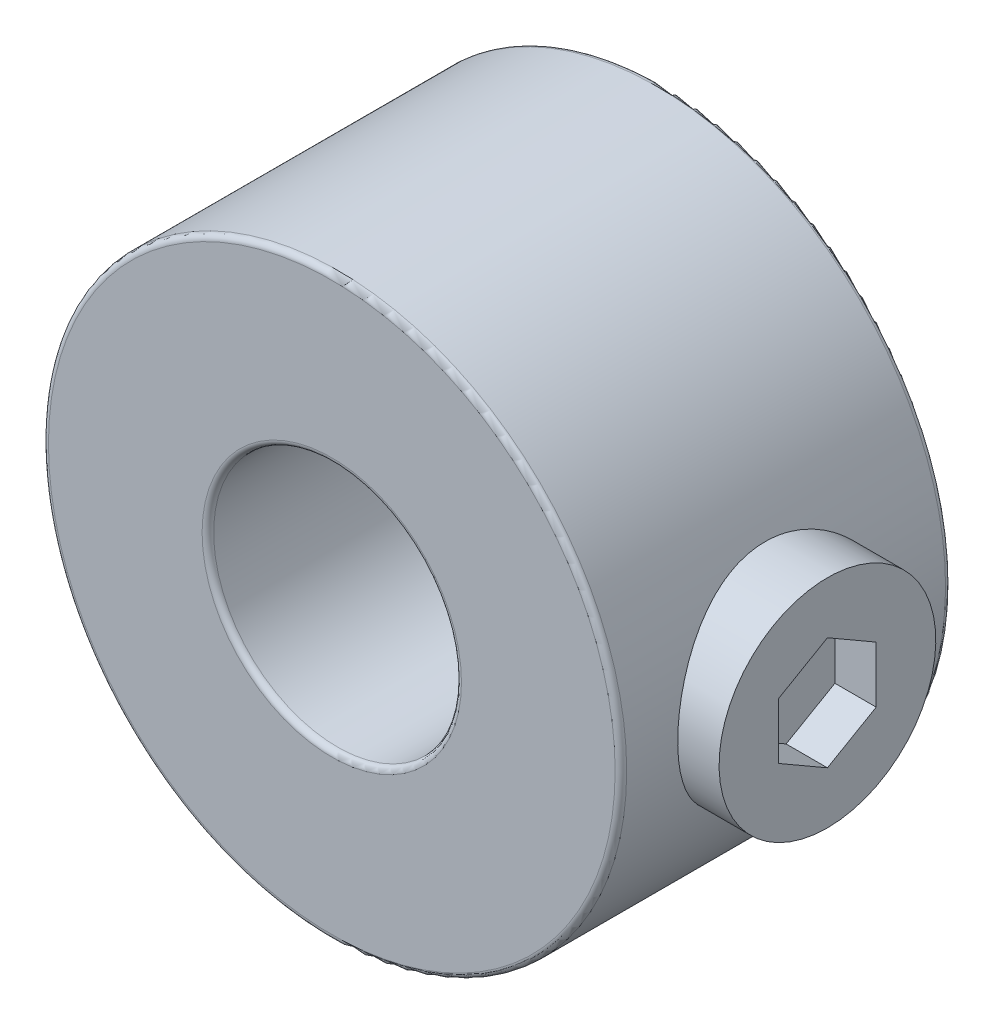
SolidWorks part; units mm, degrees
ref_plane "Front Plane" through (0, 0, 0) normal (0, 0, 1) x (1, 0, 0)
ref_plane "Top Plane" through (0, 0, 0) normal (0, 1, 0) x (1, 0, 0)
ref_plane "Right Plane" through (0, 0, 0) normal (1, 0, 0) x (0, 0, -1)
sketch "Sketch1" plane through (0, 0, 0) normal (0, 0, 1) x (1, 0, 0)
  circle A0 centre (0, 0) radius 5.5562
  circle A1 centre (0, 0) radius 2.3813
  point P4 (5.5562, 0)
  dimension "Bore Dia" = 4.7625
  dimension "OD" = 11.1125
extrude "Extrude1" add sketch "Sketch1" along normal blind 6.35
ref_plane "Plane1" through (5.5562, 0, 0) normal (1, 0, 0) x (0, 0, -1)
sketch "Sketch2" plane through (5.5562, 0, 0) normal (1, 0, 0) x (0, 0, -1)
  line L0 (0, 0) -> (-6.35, 0) construction
  line L1 (-6.35, 5.5562) -> (-6.35, -5.5562) construction
  circle A0 centre (-3.175, 0) radius 2.0828
  dimension "Set Screw Dia" = 4.1656
extrude "Cut-Extrude1" cut sketch "Sketch2" against normal up to surface (5.5562 mm away) up to plane "Right Plane"
ref_plane "Plane2" through (0, 0, 3.175) normal (0, 0, 1) x (1, 0, 0)
sketch "Sketch3" plane through (0, 0, 3.175) normal (0, 0, 1) x (1, 0, 0)
  line L1 (3.175, 0) -> (6.35, 0)
  line L2 (3.175, 0) -> (3.175, 2.0828)
  line L3 (3.175, 2.0828) -> (6.35, 2.0828)
  line L4 (6.35, 0) -> (6.35, 2.0828)
  line L5 (3.175, 0) -> (0, 0) construction
  dimension "D1" = 3.175
  dimension "D2" = 0.7937
  dimension "D3" = 4.1656
revolve "Revolve1" add sketch "Sketch3" angle 360 about L1
sketch "Sketch4" plane through (6.35, 0, 0) normal (1, 0, 0) x (0, 0, -1)
  line L1 (-3.175, 1.0823) -> (-4.1123, 0.5411)
  line L2 (-4.1123, 0.5411) -> (-4.1123, -0.5411)
  line L3 (-4.1123, -0.5411) -> (-3.175, -1.0823)
  line L4 (-3.175, -1.0823) -> (-2.2377, -0.5411)
  line L5 (-2.2377, -0.5411) -> (-2.2377, 0.5411)
  line L6 (-2.2377, 0.5411) -> (-3.175, 1.0823)
  circle A0 centre (-3.175, 0) radius 0.9373 construction
  dimension "D1" = 1.8745
extrude "Cut-Extrude2" cut sketch "Sketch4" against normal up to vertex (0.7937 mm away) up to point (5.5562, 0, 3.175)
fillet "Fillet1" radius 0.1111 4 edges at (2.3813, 0, 0) (2.3813, 0, 6.35) (5.5562, 0, 0) (5.5562, 0, 6.35)
equation "\"D1@Sketch3\" = (\"OD@Sketch1\"-\"Bore Dia@Sketch1\")/2"
equation "\"D2@Sketch3\" = \"D1@Sketch3\"/4"
equation "\"D1@Sketch4\" = \"Set Screw Dia@Sketch2\"*.45"
equation "\"D3@Sketch3\" = \"Set Screw Dia@Sketch2\""
equation "\"D1@Fillet1\" = \"OD@Sketch1\"*.01"
